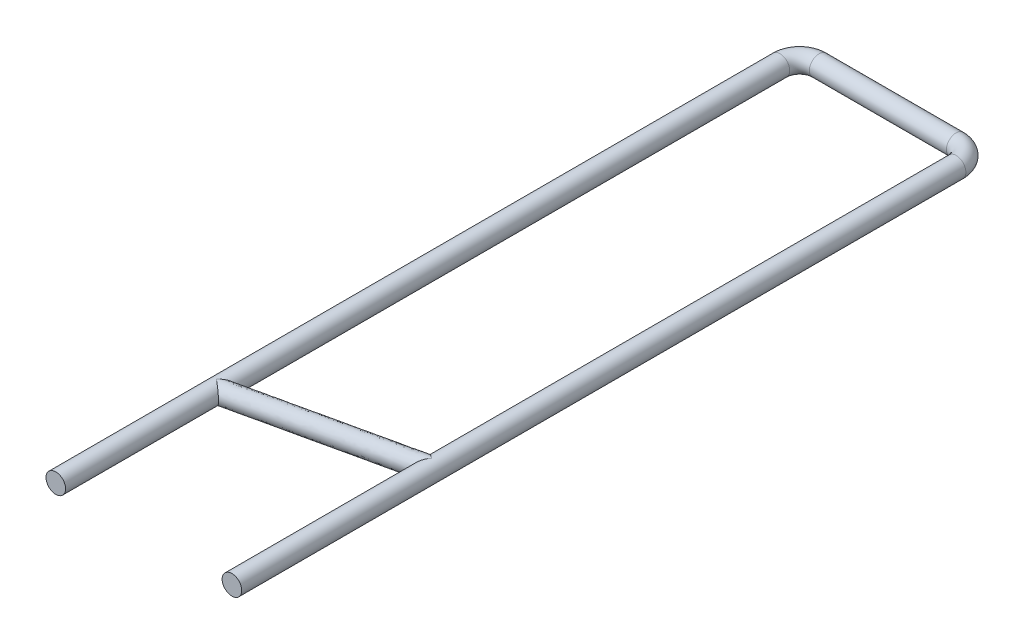
SolidWorks part; units mm, degrees
ref_plane "前基準面" through (0, 0, 0) normal (0, 0, 1) x (1, 0, 0)
ref_plane "上基準面" through (0, 0, 0) normal (0, 1, 0) x (1, 0, 0)
ref_plane "右基準面" through (0, 0, 0) normal (1, 0, 0) x (0, 0, -1)
sketch "草圖1" plane through (0, 0, 38) normal (0, 0, 1) x (1, 0, 0)
  circle A0 centre (-4.5, 0) radius 0.5
  dimension "D1" = 1
sketch "草圖2" plane through (0, 0, 0) normal (0, 1, 0) x (1, 0, 0)
  line L0 (-4.5, -38) -> (-4.5, -1)
  line L1 (-3.5, 0) -> (3.5, 0)
  line L2 (4.5, -1) -> (4.5, -38)
  arc A0 (-4.5, -1) -> (-3.5, 0) centre (-3.5, -1) cw
  arc A1 (3.5, 0) -> (4.5, -1) centre (3.5, -1) cw
sweep "掃出1" add profiles "草圖1" path "草圖2"
sketch "草圖3" plane through (4.5, 0, 0) normal (1, 0, 0) x (0, 0, -1)
  circle A0 centre (-27.8, 0) radius 0.5
  dimension "D1" = 1
sketch "草圖4" plane through (0, 0, 0) normal (0, 1, 0) x (1, 0, 0)
  line L0 (-4.5, -29.8) -> (4.5, -27.8)
sweep "掃出2" add profiles "草圖3" path "草圖4"
